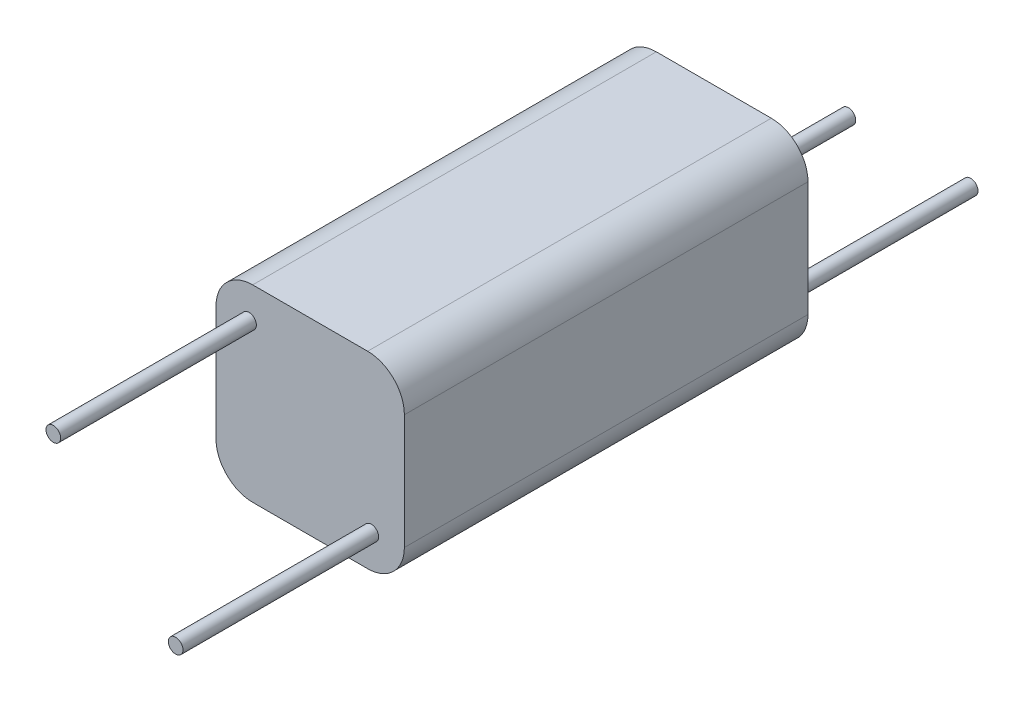
SolidWorks part; units mm, degrees
ref_plane "Спереди" through (0, 0, 0) normal (0, 0, 1) x (1, 0, 0)
ref_plane "Сверху" through (0, 0, 0) normal (0, 1, 0) x (1, 0, 0)
ref_plane "Справа" through (0, 0, 0) normal (1, 0, 0) x (0, 0, -1)
sketch "Эскиз1" plane through (0, 0, 0) normal (0, 0, 1) x (1, 0, 0)
  line L1 (-2.35, -3.85) -> (2.35, -3.85)
  line L2 (-3.85, -2.35) -> (-3.85, 2.35)
  line L3 (-2.35, 3.85) -> (2.35, 3.85)
  line L4 (3.85, -2.35) -> (3.85, 2.35)
  line L5 (-3.85, -3.85) -> (3.85, 3.85) construction
  line L6 (-3.85, 3.85) -> (3.85, -3.85) construction
  arc A0 (-3.85, -2.35) -> (-2.35, -3.85) centre (-2.35, -2.35) ccw
  arc A1 (2.35, -3.85) -> (3.85, -2.35) centre (2.35, -2.35) ccw
  arc A2 (2.35, 3.85) -> (3.85, 2.35) centre (2.35, 2.35) cw
  arc A3 (-2.35, 3.85) -> (-3.85, 2.35) centre (-2.35, 2.35) ccw
  point P0 (0, 0)
  dimension "D1" = 1.5
  dimension "D2" = 7.7
  dimension "D3" = 7.7
extrude "Бобышка-Вытянуть1" add sketch "Эскиз1" along normal blind 16.5
sketch "Эскиз2" plane through (0, 0, 0) normal (0, 0, -1) x (-1, 0, 0)
  circle A0 centre (-2.5, -2.5) radius 0.3
  circle A1 centre (2.5, -2.5) radius 0.3
  dimension "D1" = 5
  dimension "D3" = 2.5
  dimension "D4" = 0.6
  dimension "D2" = 2.5
extrude "Бобышка-Вытянуть2" add sketch "Эскиз2" along normal blind 8
sketch "Эскиз3" plane through (0, 0, 16.5) normal (0, 0, 1) x (1, 0, 0)
  circle A0 centre (2.5, -2.5) radius 0.3
  circle A1 centre (-2.5, 2.5) radius 0.3
  circle A2 centre (2.5, -2.5) radius 0.3 construction
  dimension "D1" = 5
  dimension "D2" = 5
extrude "Бобышка-Вытянуть3" add sketch "Эскиз3" along normal blind 8
